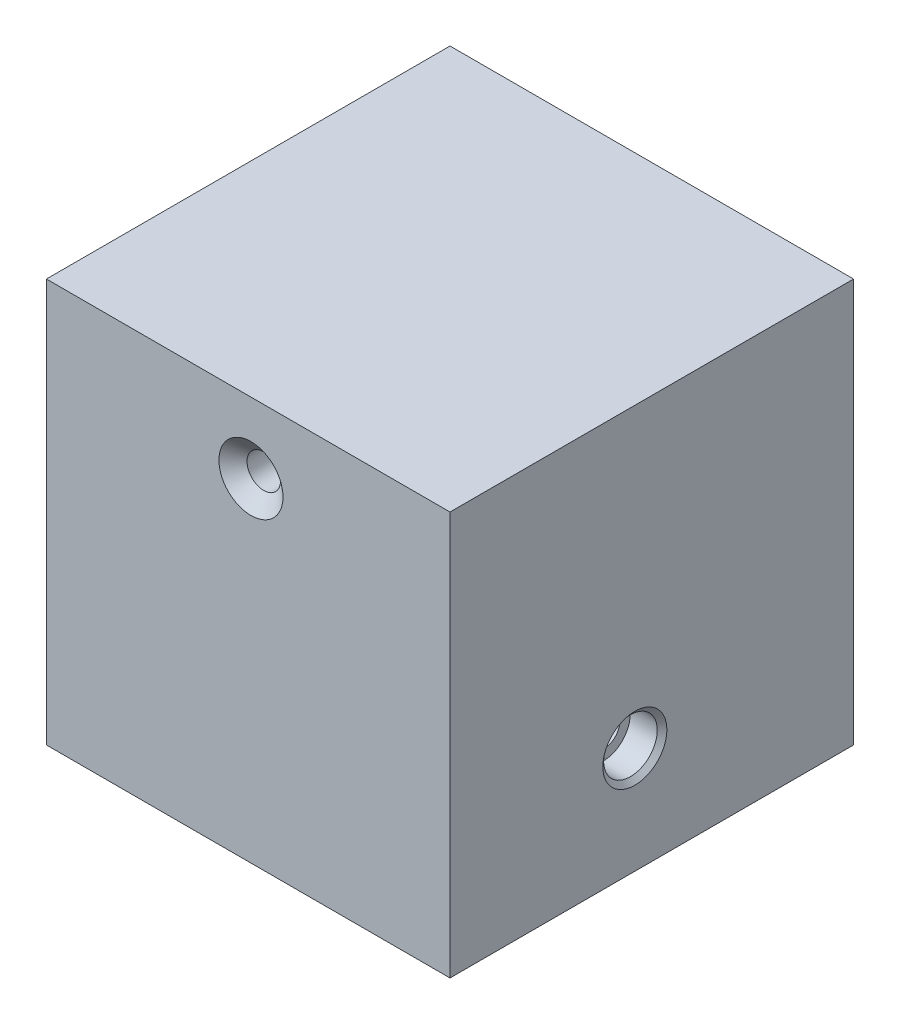
SolidWorks part; units mm, degrees
ref_plane "Front" through (0, 0, 0) normal (0, 0, 1) x (1, 0, 0)
ref_plane "Top" through (0, 0, 0) normal (0, 1, 0) x (1, 0, 0)
ref_plane "Right" through (0, 0, 0) normal (1, 0, 0) x (0, 0, -1)
sketch "Sketch1" plane through (0, 0, 0) normal (0, 0, 1) x (1, 0, 0)
  line L1 (0, 0) -> (101.6, 0)
  line L2 (0, 0) -> (0, 101.6)
  line L3 (0, 101.6) -> (101.6, 101.6)
  line L4 (101.6, 0) -> (101.6, 101.6)
  dimension "D1" = 101.6
  dimension "D2" = 101.6
extrude "Boss-Extrude1" add sketch "Sketch1" along normal blind 101.6
hole_wizard "CSK for 5/16 Flat Head Machine Screw (100)1" positions "Sketch2" profile "Sketch3" countersink size "5/16" standard "ANSI Inch" end condition through all
sketch "Sketch2" plane through (0, 0, 101.6) normal (0, 0, 1) x (1, 0, 0)
  point P0 (51.4901, 83.8415)
sketch "Sketch3" plane through (51.4901, 83.8415, 101.6) normal (1, 0, 0) x (0, -1, 0)
  line L0 (0, 0) -> (0, 101.6)
  line L1 (0, 101.6) -> (8.0645, 101.6)
  line L2 (4.2164, 98.3711) -> (4.2164, 3.2289)
  line L3 (4.2164, 3.2289) -> (8.0645, 0)
  line L5 (8.0645, 0) -> (0, 0)
  line L6 (-4.2164, 3.2289) -> (-8.0645, 0) construction
  line L7 (8.0645, 101.6) -> (4.2164, 98.3711)
  line L8 (-8.0645, 101.6) -> (-4.2164, 98.3711) construction
  line L11 (0, -6.35) -> (0, 107.95) construction
  dimension "Thru Hole Dia." = 8.4328
  dimension "Thru Hole Depth" = 101.6
  dimension "Near C'Sink Dia." = 16.129
  dimension "Near C'Sink Angle" = 100
  dimension "Far C'Sink Dia." = 16.129
  dimension "Far C'Sink Angle" = 100
hole_wizard "CBORE for 5/16 Socket Head Cap Screw1" positions "Sketch4" profile "Sketch5" counterbore size "5/16" standard "ANSI Inch" end condition through all
sketch "Sketch4" plane through (101.6, 0, 0) normal (1, 0, 0) x (0, 0, -1)
  point P0 (-55.0625, 26.8232)
sketch "Sketch5" plane through (101.6, 26.8232, 55.0625) normal (0, 1, 0) x (0, 0, -1)
  line L0 (0, 0) -> (0, 101.6)
  line L1 (0, 101.6) -> (4.2164, 101.6)
  line L3 (4.2164, 101.6) -> (4.2164, 7.9375)
  line L4 (6.7475, 7.9375) -> (4.2164, 7.9375)
  line L5 (6.7475, 7.9375) -> (6.7475, 1.1051)
  line L6 (6.7475, 1.1051) -> (8.0645, 0)
  line L7 (8.0645, 0) -> (0, 0)
  line L8 (-6.7475, 1.1051) -> (-8.0645, 0) construction
  line L11 (0, -6.35) -> (0, 107.95) construction
  dimension "Thru Hole Dia." = 8.4328
  dimension "Thru Hole Depth" = 101.6
  dimension "C'Bore Dia." = 13.495
  dimension "C'Bore Depth" = 7.9375
  dimension "Near C'Sink Dia." = 16.129
  dimension "Near C'Sink Angle" = 100
sketch "Sketch6" plane through (0, 0, 0) normal (-1, 0, 0) x (0, 0, 1)
  circle A0 centre (55.0625, 26.8232) radius 6.9228
extrude "Cut-Extrude1" cut sketch "Sketch6" against normal blind 12.7
chamfer "Chamfer2" distance 2.54 angle 45 1 edges at (0, 26.8232, 61.9853)
ref_plane "Plane1" through (50.8, 0, 0) normal (1, 0, 0) x (0, 0, -1)
sketch "Sketch7" plane through (50.8, 0, 0) normal (1, 0, 0) x (0, 0, -1)
  circle A0 centre (-55.0625, 26.8232) radius 4.2164 construction
  circle A1 centre (-55.0625, 26.8232) radius 4.2164
extrude "Boss-Extrude2" add sketch "Sketch7" along normal mid plane 0.254
